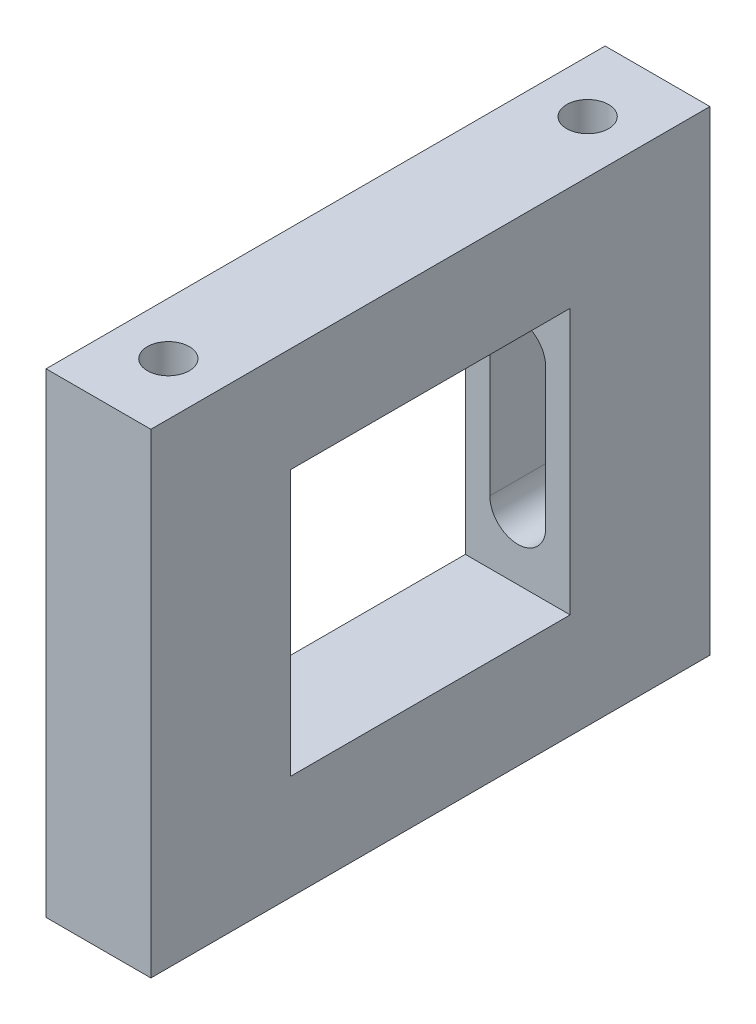
SolidWorks part; units mm, degrees
material "ABS"
ref_plane "Plano frontal" through (0, 0, 0) normal (0, 0, 1) x (1, 0, 0)
ref_plane "Plano superior" through (0, 0, 0) normal (0, 1, 0) x (1, 0, 0)
ref_plane "Plano direito" through (0, 0, 0) normal (1, 0, 0) x (0, 0, -1)
sketch "Esboço1" plane through (0, 0, 0) normal (0, 0, 1) x (1, 0, 0)
  line L0 (0, -40.8772) -> (0, 59.4737) construction
  line L2 (-52.5, -7.5) -> (-67.5, -7.5)
  line L3 (-52.5, -7.5) -> (-52.5, 7.5)
  line L4 (-52.5, 7.5) -> (-67.5, 7.5)
  line L5 (-67.5, -7.5) -> (-67.5, 7.5)
  line L6 (-52.5, -7.5) -> (-67.5, 7.5) construction
  line L7 (-52.5, 7.5) -> (-67.5, -7.5) construction
  point P3 (-60, 0)
  dimension "D1" = 15
  dimension "D2" = 15
  dimension "D3" = 60
extrude "Ressalto-extrusão1" add sketch "Esboço1" along normal blind 80
sketch "Esboço2" plane through (0, 7.5, 0) normal (0, 1, 0) x (1, 0, 0)
  line L0 (0, 13.0797) -> (0, -105.8822) construction
  line L1 (-52.5, -80) -> (-52.5, 0) construction
  line L2 (-67.5, 0) -> (-52.5, 0)
  line L3 (-67.5, 0) -> (-67.5, -20)
  line L4 (-67.5, -20) -> (-52.5, -20)
  line L5 (-52.5, 0) -> (-52.5, -20)
  line L6 (-85.1046, -40) -> (42.413, -40) construction
  line L7 (-52.5, -80) -> (-52.5, -60)
  line L8 (-67.5, -60) -> (-52.5, -60)
  line L9 (-67.5, -80) -> (-67.5, -60)
  line L10 (-67.5, -80) -> (-52.5, -80)
  dimension "D1" = 20
extrude "Ressalto-extrusão2" add sketch "Esboço2" along normal blind 53
sketch "Esboço4" plane through (0, 0, 20) normal (0, 0, 1) x (1, 0, 0)
  line L0 (-60, 159.1955) -> (-60, -43.7803) construction
  line L1 (-67.5, 26.5) -> (-52.5, 26.5) construction
  line L2 (-67.5, 60.5) -> (-67.5, 7.5) construction
  line L3 (-52.5, 60.5) -> (-52.5, 7.5) construction
  line L4 (-67.5, 7.5) -> (-52.5, 7.5) construction
  line L5 (-60, 36.5) -> (-60, 16.5) construction
  line L6 (-56, 36.5) -> (-56, 16.5)
  line L7 (-64, 36.5) -> (-64, 16.5)
  arc A0 (-56, 36.5) -> (-64, 36.5) centre (-60, 36.5) ccw
  arc A1 (-64, 16.5) -> (-56, 16.5) centre (-60, 16.5) ccw
  point P12 (-60, 26.5)
  dimension "D1" = 19
  dimension "D2" = 20
  dimension "D3" = 8
extrude "Corte-extrusão1" cut sketch "Esboço4" against normal through all
sketch "Esboço5" plane through (0, 60.5, 0) normal (0, 1, 0) x (1, 0, 0)
  line L0 (-60, 9.7559) -> (-60, -87.3229) construction
  line L1 (-79.2211, -40) -> (-35.4262, -40) construction
  line L2 (-67.5, -10) -> (-52.5, -10) construction
  line L3 (-67.5, 0) -> (-67.5, -20) construction
  line L4 (-52.5, -20) -> (-52.5, 0) construction
  circle A0 centre (-60, -10) radius 3
  circle A1 centre (-60, -70) radius 3
  dimension "D1" = 6
extrude "Corte-extrusão2" cut sketch "Esboço5" against normal blind 16.5
sketch "Esboço6" plane through (0, 0, 20) normal (0, 0, 1) x (1, 0, 0)
  line L0 (-52.5, 60.5) -> (-52.5, 7.5) construction
  line L1 (-67.5, 60.5) -> (-52.5, 60.5)
  line L2 (-67.5, 60.5) -> (-67.5, 45.5)
  line L3 (-67.5, 45.5) -> (-52.5, 45.5)
  line L4 (-52.5, 60.5) -> (-52.5, 45.5)
  dimension "D1" = 15
extrude "Ressalto-extrusão3" add sketch "Esboço6" along normal blind 40
